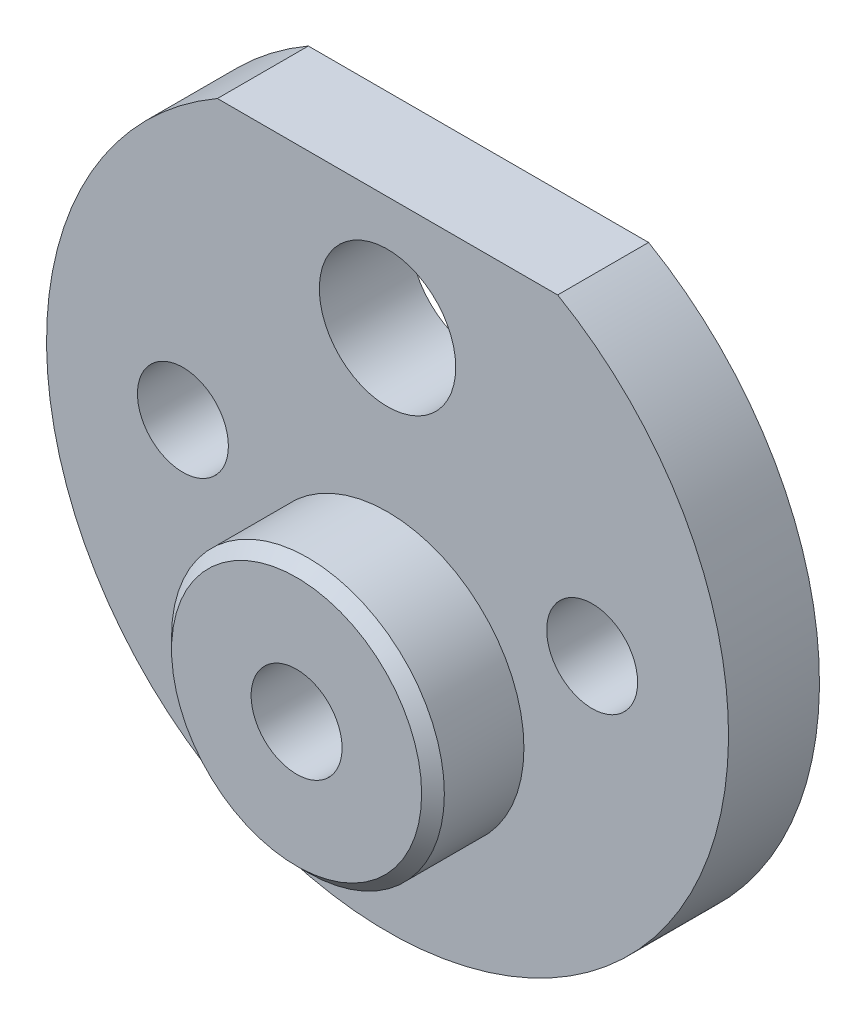
SolidWorks part; units mm, degrees
ref_plane "Front Plane" through (0, 0, 0) normal (0, 0, 1) x (1, 0, 0)
ref_plane "Top Plane" through (0, 0, 0) normal (0, 1, 0) x (1, 0, 0)
ref_plane "Right Plane" through (0, 0, 0) normal (1, 0, 0) x (0, 0, -1)
sketch "Sketch1" plane through (0, 0, 0) normal (0, 0, 1) x (1, 0, 0)
  line L0 (-7.4833, 13) -> (7.4833, 13)
  line L1 (0, 10.4385) -> (0, 0) construction
  arc A0 (-7.4833, 13) -> (7.4833, 13) centre (0, 0) ccw
  circle A1 centre (0, 8) radius 3
  circle A2 centre (-9, 0) radius 2
  circle A3 centre (9, 0) radius 2
  dimension "D1" = 30
  dimension "D3" = 6
  dimension "D5" = 4
  dimension "D2" = 13
  dimension "D4" = 8
  dimension "D6" = 9
  dimension "D7" = 9
extrude "Boss-Extrude1" add sketch "Sketch1" along normal blind 4
sketch "Sketch2" plane through (0, 0, 4) normal (0, 0, 1) x (1, 0, 0)
  circle A0 centre (0, -5) radius 6
  dimension "D2" = 12
  dimension "D1" = 5
extrude "Boss-Extrude2" add sketch "Sketch2" along normal blind 4
sketch "Sketch3" plane through (0, 0, 8) normal (0, 0, 1) x (1, 0, 0)
  circle A0 centre (0, -5) radius 2
  dimension "D1" = 4
extrude "Cut-Extrude1" cut sketch "Sketch3" against normal through all
chamfer "Chamfer1" distance 0.5 angle 45 1 edges at (6, -5, 8)
